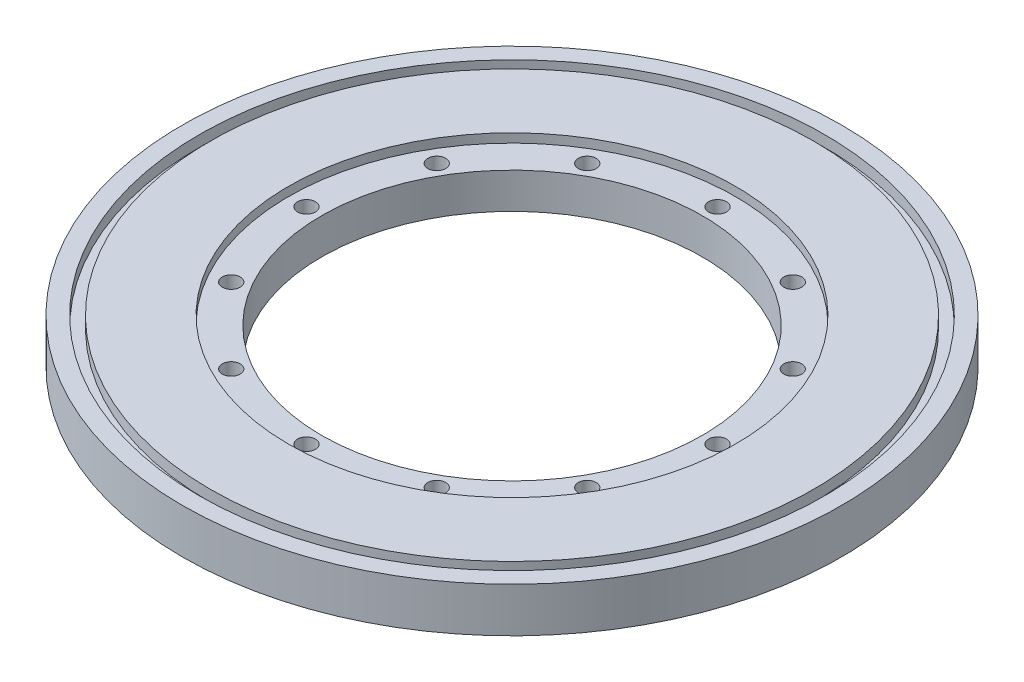
SolidWorks part; units mm, degrees
ref_plane "Front Plane" through (0, 0, 0) normal (0, 0, 1) x (1, 0, 0)
ref_plane "Top Plane" through (0, 0, 0) normal (0, 1, 0) x (1, 0, 0)
ref_plane "Right Plane" through (0, 0, 0) normal (1, 0, 0) x (0, 0, -1)
sketch "Sketch1" plane through (0, 0, 0) normal (0, 1, 0) x (1, 0, 0)
  circle A0 centre (0, 0) radius 93.6625
  dimension "D1" = 187.325
extrude "Boss-Extrude1" add sketch "Sketch1" along normal blind 12.7
sketch "Sketch2" plane through (0, 12.7, 0) normal (0, 1, 0) x (1, 0, 0)
  circle A0 centre (0, 0) radius 54.102
  dimension "D1" = 108.204
extrude "Cut-Extrude1" cut sketch "Sketch2" against normal through all
sketch "Sketch3" plane through (0, 12.7, 0) normal (0, 1, 0) x (1, 0, 0)
  circle A0 centre (0, 0) radius 63.5
  dimension "D1" = 127
extrude "Cut-Extrude2" cut sketch "Sketch3" against normal blind 2.54
sketch "Sketch4" plane through (0, 12.7, 0) normal (0, 1, 0) x (1, 0, 0)
  circle A0 centre (0, 58.42) radius 2.54
  dimension "D1" = 5.08
  dimension "D2" = 58.42
extrude "Cut-Extrude3" cut sketch "Sketch4" against normal through all
pattern_circular "CirPattern1" count 12 over 360 about axis through (0, 0, 0) along (0, 1, 0) of "Cut-Extrude3"
sketch "Sketch5" plane through (0, 12.7, 0) normal (0, 1, 0) x (1, 0, 0)
  circle A0 centre (0, 0) radius 85.725
  circle A1 centre (0, 0) radius 88.9
  dimension "D1" = 171.45
  dimension "D2" = 177.8
extrude "Cut-Extrude4" cut sketch "Sketch5" against normal blind 3.175
